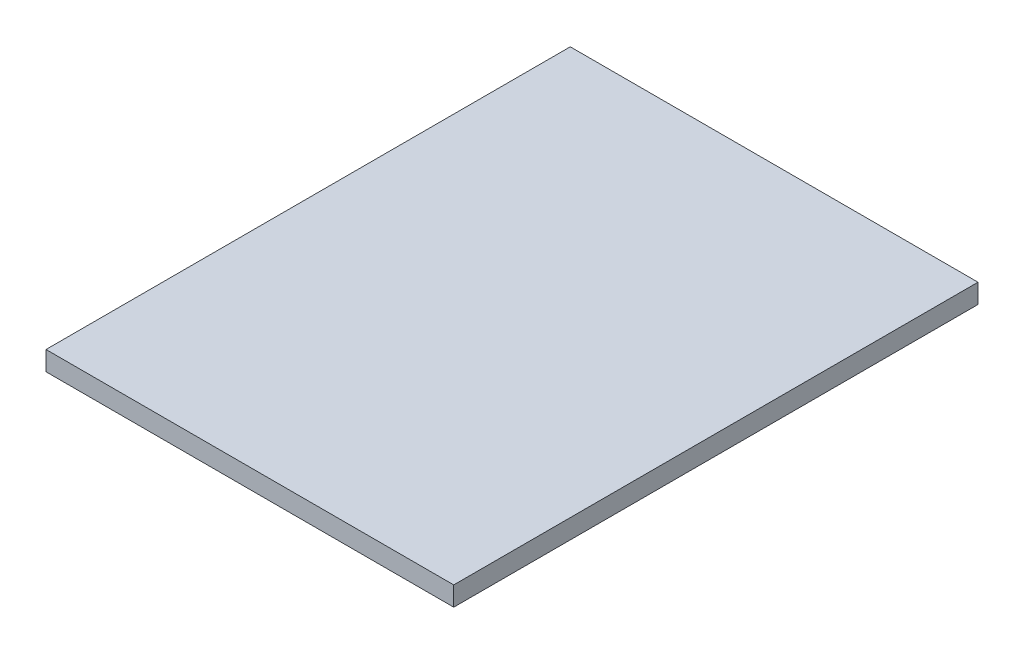
SolidWorks part; units mm, degrees
ref_plane "Front Plane" through (0, 0, 0) normal (0, 0, 1) x (1, 0, 0)
ref_plane "Top Plane" through (0, 0, 0) normal (0, 1, 0) x (1, 0, 0)
ref_plane "Right Plane" through (0, 0, 0) normal (1, 0, 0) x (0, 0, -1)
sketch "Sketch1" plane through (0, 0, 0) normal (0, 1, 0) x (1, 0, 0)
  line L1 (0, 0) -> (53.594, 0)
  line L2 (0, 0) -> (0, 68.9102)
  line L3 (0, 68.9102) -> (53.594, 68.9102)
  line L4 (53.594, 0) -> (53.594, 68.9102)
  dimension "D1" = 68.9102
  dimension "D2" = 53.594
extrude "Boss-Extrude1" add sketch "Sketch1" along normal blind 2.54
